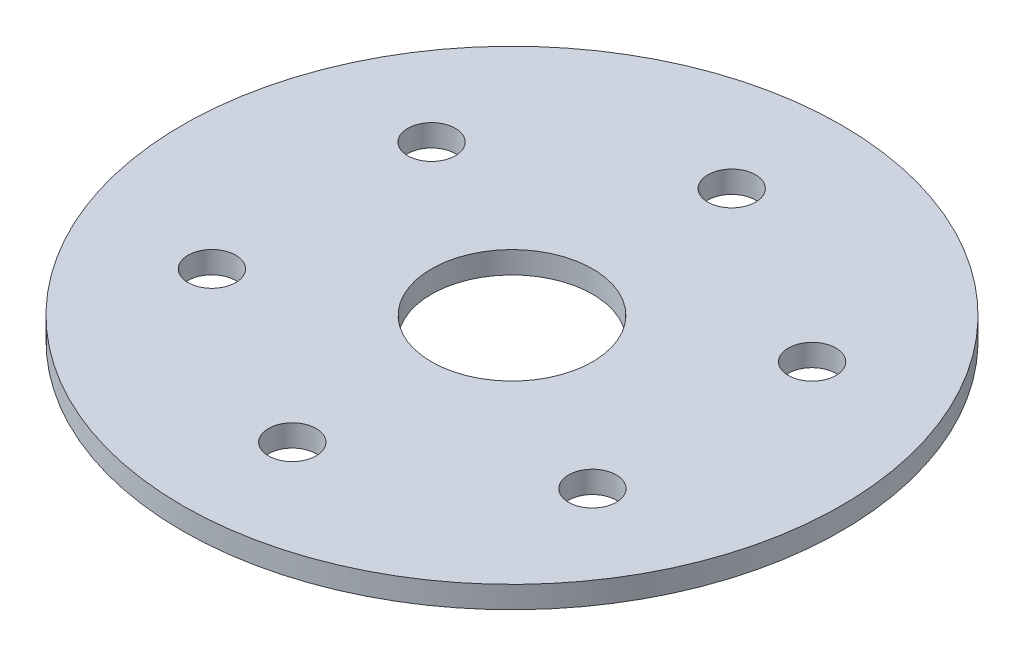
SolidWorks part; units mm, degrees
ref_plane "Alzado" through (0, 0, 0) normal (0, 0, 1) x (1, 0, 0)
ref_plane "Planta" through (0, 0, 0) normal (0, 1, 0) x (1, 0, 0)
ref_plane "Vista lateral" through (0, 0, 0) normal (1, 0, 0) x (0, 0, -1)
sketch "Croquis1" plane through (0, 0, 0) normal (0, 1, 0) x (1, 0, 0)
  circle A0 centre (0, 0) radius 11
  circle A1 centre (0, 0) radius 45
  dimension "D1" = 22
  dimension "D2" = 90
extrude "Saliente-Extruir1" add sketch "Croquis1" along normal blind 3
sketch "Croquis2" plane through (0, 3, 0) normal (0, 1, 0) x (1, 0, 0)
  line L0 (0, 0) -> (0, 156.286) construction
  circle A0 centre (0, 30) radius 3.25
  circle A1 centre (25.9808, 15) radius 3.25
  circle A2 centre (25.9808, -15) radius 3.25
  circle A3 centre (0, -30) radius 3.25
  circle A4 centre (-25.9808, -15) radius 3.25
  circle A5 centre (-25.9808, 15) radius 3.25
  point P18 (0, 0)
  dimension "D1" = 6.5
  dimension "D2" = 30
  dimension "D3" = 6
extrude "Cortar-Extruir1" cut sketch "Croquis2" against normal through all
